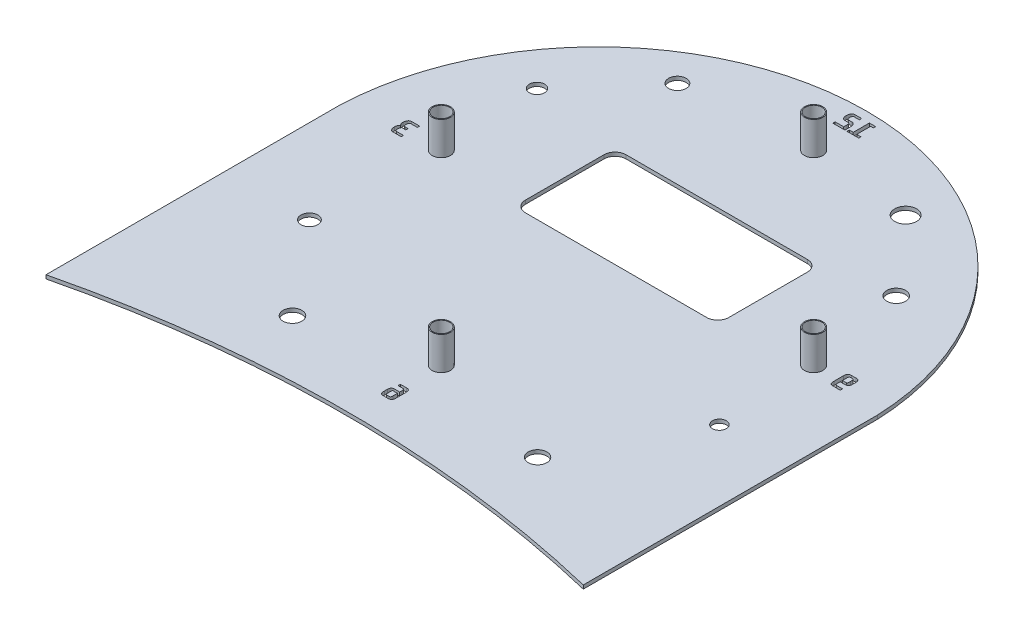
SolidWorks part; units mm, degrees
ref_plane "Front Plane" through (0, 0, 0) normal (0, 0, 1) x (1, 0, 0)
ref_plane "Top Plane" through (0, 0, 0) normal (0, 1, 0) x (1, 0, 0)
ref_plane "Right Plane" through (0, 0, 0) normal (1, 0, 0) x (0, 0, -1)
sketch "Sketch2" plane through (0, 0, 0) normal (0, 1, 0) x (1, 0, 0)
  line L0 (0, 0) -> (0, 50.59) construction
  line L1 (0, 0) -> (-50.59, 0) construction
  line L2 (0, 0) -> (0, -50.59) construction
  line L3 (0, 0) -> (50.59, 0) construction
  circle A0 centre (0, 50.59) radius 2.5
  circle A1 centre (0, -50.59) radius 2.5
  circle A2 centre (-50.59, 0) radius 2.5
  circle A3 centre (50.59, 0) radius 2.5
  dimension "D5" = 5
  dimension "D6" = 5
extrude "Boss-Extrude1" add sketch "Sketch2" along normal blind 10
sketch "Sketch3" plane through (0, 0, 0) normal (0, 1, 0) x (1, 0, 0)
  line L0 (-61.4941, 0) -> (61.4941, 0) construction
  line L1 (0, 50.59) -> (0, 75.59) construction
  line L2 (-75, 0) -> (75, 0) construction
  line L5 (-75, -3) -> (-75, -83)
  line L7 (71, -3) -> (71, -83)
  line L15 (-75, -3) -> (-75, 67) construction
  line L16 (-75, 67) -> (87.3672, 67) construction
  arc A3 (-75, -3) -> (71, -3) centre (-2, -6.0643) cw
  arc A4 (-75, -83) -> (71, -83) centre (-2, -384.7867) cw
  point P3 (0, 0)
  point P9 (0, 0)
  dimension "D1" = 70
  dimension "D2" = 80
  dimension "D3" = 146
extrude "Boss-Extrude3" add sketch "Sketch3" along normal blind 1
sketch "Sketch4" plane through (0, 1, 0) normal (0, 1, 0) x (1, 0, 0)
  line L0 (-50.59, 0) -> (-27.4274, 0) construction
  line L8 (50.8371, 0) -> (27.8349, 0) construction
  line L9 (-27.4274, -3.2969) -> (-27.4274, 24.0477) construction
  line L10 (-27.4274, 24.0477) -> (27.8349, 24.0477) construction
  line L11 (27.8349, 24.0477) -> (27.8349, 0) construction
  line L12 (27.8349, -3.2969) -> (-27.4274, -3.2969) construction
  line L14 (-24.4274, 24.0477) -> (24.8349, 24.0477)
  line L15 (-27.4274, 21.0477) -> (-27.4274, -0.2969)
  line L16 (-24.4274, -3.2969) -> (24.8349, -3.2969)
  line L17 (27.8349, 21.0477) -> (27.8349, -0.2969)
  arc A2 (-24.4274, 24.0477) -> (-27.4274, 21.0477) centre (-24.4274, 21.0477) ccw
  arc A3 (-27.4274, -0.2969) -> (-24.4274, -3.2969) centre (-24.4274, -0.2969) ccw
  arc A4 (24.8349, -3.2969) -> (27.8349, -0.2969) centre (24.8349, -0.2969) ccw
  arc A5 (27.8349, 21.0477) -> (24.8349, 24.0477) centre (24.8349, 21.0477) ccw
  dimension "D1" = 3
extrude "Cut-Extrude1" cut sketch "Sketch4" against normal through all
sketch "Sketch6" plane through (0, 10, 0) normal (0, 1, 0) x (1, 0, 0)
  circle A0 centre (0, 50.59) radius 2.25
  circle A1 centre (50.59, 0) radius 2.25
  circle A2 centre (0, -50.59) radius 2.25
  circle A3 centre (-50.59, 0) radius 2.25
  dimension "D1" = 4.5
extrude "Cut-Extrude2" cut sketch "Sketch6" against normal blind 7
sketch "Sketch8" plane through (0, 1, 0) normal (0, 1, 0) x (1, 0, 0)
  circle A0 centre (-34.2416, 47.8177) radius 2.385
  circle A1 centre (-52.129, 27.5453) radius 2.0584
  circle A3 centre (-31.8566, -59.1661) radius 2.5553
  circle A4 centre (34.7527, -59.1661) radius 2.5325
  circle A5 centre (51.7883, -26.7984) radius 1.8739
  circle A6 centre (-52.129, -34.2941) radius 2.2919
  circle A8 centre (27.7681, 47.8177) radius 2.9751
  circle A9 centre (45.4851, 27.5453) radius 2.5553
  text T0 "12" font "Unispace" height 5
  text T1 "3" font "Unispace" height 5
  text T2 "6" font "Unispace" height 5
  text T3 "9" font "Unispace" height 5
extrude "Cut-Extrude3" cut sketch "Sketch8" against normal through all
